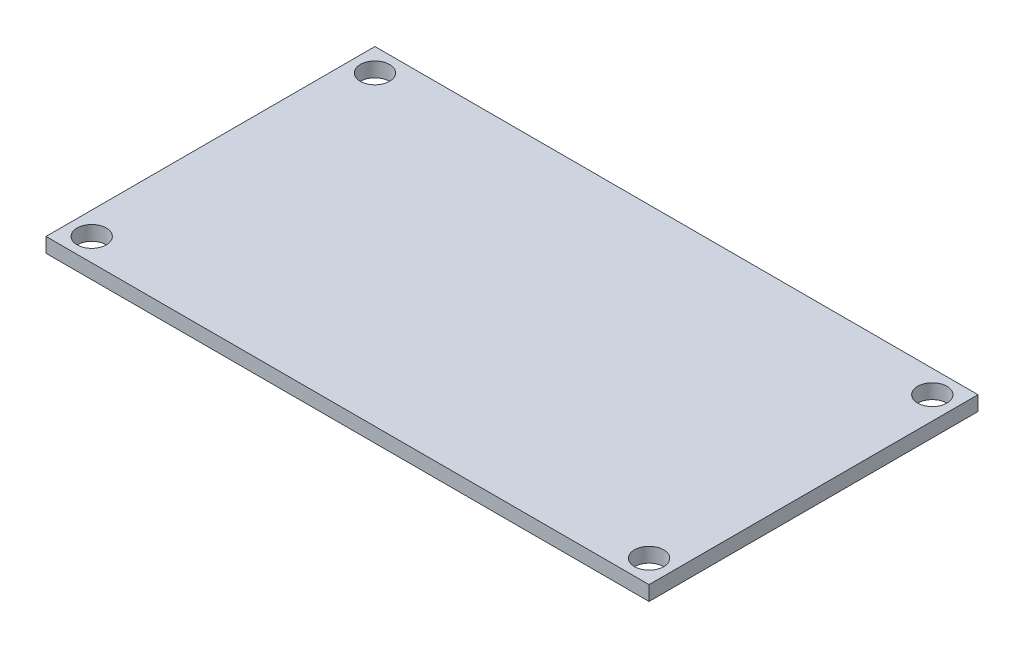
SolidWorks part; units mm, degrees
ref_plane "Front Plane" through (0, 0, 0) normal (0, 0, 1) x (1, 0, 0)
ref_plane "Top Plane" through (0, 0, 0) normal (0, 1, 0) x (1, 0, 0)
ref_plane "Right Plane" through (0, 0, 0) normal (1, 0, 0) x (0, 0, -1)
sketch "Sketch1" plane through (0, 0, 0) normal (0, 1, 0) x (1, 0, 0)
  line L1 (-33, 18) -> (33, 18)
  line L2 (-33, 18) -> (-33, -18)
  line L3 (-33, -18) -> (33, -18)
  line L4 (33, 18) -> (33, -18)
  line L5 (-33, 18) -> (33, -18) construction
  line L6 (-33, -18) -> (33, 18) construction
  point P0 (0, 0)
  dimension "D1" = 36
  dimension "D2" = 66
extrude "Boss-Extrude1" add sketch "Sketch1" along normal blind 1.6
hole_wizard "M3 Clearance Hole1" positions "Sketch2" profile "Sketch3" hole size "M3" standard "ANSI Metric" end condition through all
sketch "Sketch2" plane through (0, 1.6, 0) normal (0, 1, 0) x (1, 0, 0)
  point P0 (-30.5, 15.5)
  dimension "D1" = 15.5
  dimension "D2" = 30.5
sketch "Sketch3" plane through (-30.5, 1.6, -15.5) normal (1, 0, 0) x (0, 0, 1)
  line L0 (0, 0) -> (0, 1.6)
  line L1 (0, 1.6) -> (1.6, 1.6)
  line L2 (1.6, 1.6) -> (1.6, 0)
  line L5 (1.6, 0) -> (0, 0)
  line L11 (0, -6.35) -> (0, 107.95) construction
  dimension "Thru Hole Dia." = 3.2
  dimension "Thru Hole Depth" = 1.6
mirror "Mirror1" about plane through (0, 0, 0) normal (1, 0, 0) of "M3 Clearance Hole1"
mirror "Mirror2" about plane through (0, 0, 0) normal (0, 0, 1) of "Mirror1", "M3 Clearance Hole1"
